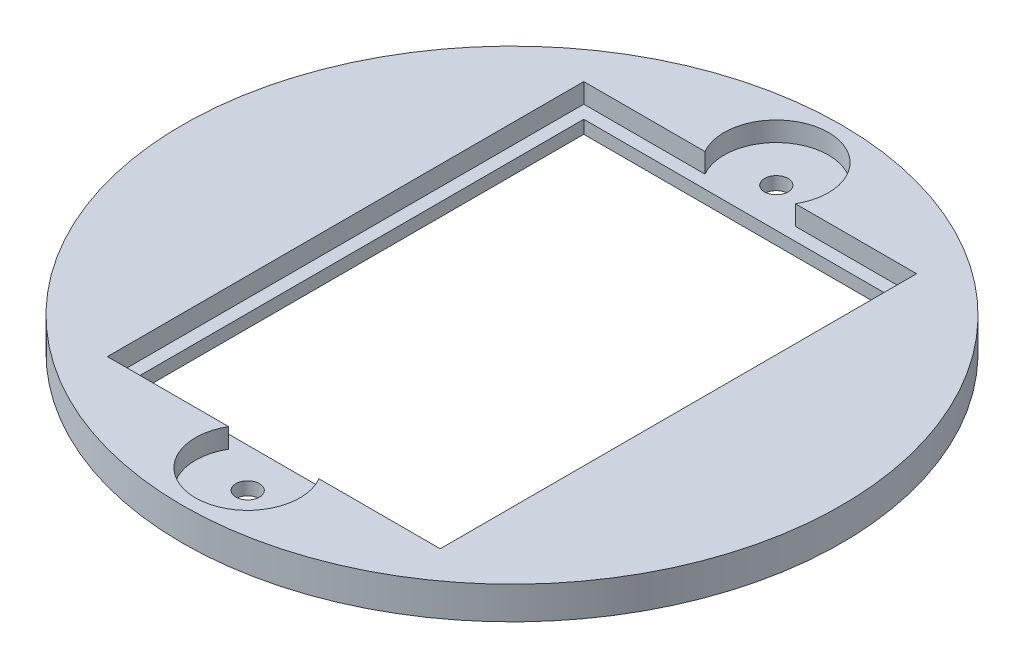
SolidWorks part; units mm, degrees
ref_plane "Front Plane" through (0, 0, 0) normal (0, 0, 1) x (1, 0, 0)
ref_plane "Top Plane" through (0, 0, 0) normal (0, 1, 0) x (1, 0, 0)
ref_plane "Right Plane" through (0, 0, 0) normal (1, 0, 0) x (0, 0, -1)
sketch "Sketch1" plane through (0, 0, 0) normal (0, 1, 0) x (1, 0, 0)
  circle A0 centre (0, 0) radius 25.25
extrude "Boss-Extrude1" add sketch "Sketch1" along normal blind 2.5
sketch "Sketch2" plane through (0, 2.5, 0) normal (0, 1, 0) x (1, 0, 0)
  line L1 (-12.75, 18.25) -> (12.75, 18.25)
  line L2 (-12.75, 18.25) -> (-12.75, -18.25)
  line L3 (-12.75, -18.25) -> (12.75, -18.25)
  line L4 (12.75, 18.25) -> (12.75, -18.25)
  line L5 (-12.75, 18.25) -> (12.75, -18.25) construction
  line L6 (-12.75, -18.25) -> (12.75, 18.25) construction
  point P0 (0, 0)
  dimension "D1" = 25.5
  dimension "D2" = 36.5
extrude "Cut-Extrude1" cut sketch "Sketch2" against normal blind 1.5
sketch "Sketch3" plane through (0, 1, 0) normal (0, 1, 0) x (1, 0, 0)
  line L1 (-11.75, 17.25) -> (11.75, 17.25)
  line L2 (-11.75, 17.25) -> (-11.75, -17.25)
  line L3 (-11.75, -17.25) -> (11.75, -17.25)
  line L4 (11.75, 17.25) -> (11.75, -17.25)
  line L5 (-11.75, 17.25) -> (11.75, -17.25) construction
  line L6 (-11.75, -17.25) -> (11.75, 17.25) construction
  point P0 (0, 0)
  dimension "D1" = 23.5
  dimension "D2" = 34.5
extrude "Cut-Extrude2" cut sketch "Sketch3" against normal blind 1.2
sketch "Sketch4" plane through (0, 2.5, 0) normal (0, 1, 0) x (1, 0, 0)
  line L0 (11.75, 17.25) -> (-11.75, 17.25) construction
  line L1 (-11.75, -17.25) -> (11.75, -17.25) construction
  circle A0 centre (0, 20.25) radius 4
  circle A1 centre (0, -20.25) radius 4
  point P4 (0, 17.25)
  point P8 (0, -17.25)
  dimension "D1" = 3
  dimension "D2" = 8
  dimension "D3" = 8
  dimension "D4" = 3
extrude "Cut-Extrude3" cut sketch "Sketch4" against normal blind 1.5
sketch "Sketch5" plane through (0, 1, 0) normal (0, 1, 0) x (1, 0, 0)
  circle A0 centre (0, 20.25) radius 0.9
  circle A1 centre (0, -20.25) radius 0.9
extrude "Cut-Extrude4" cut sketch "Sketch5" against normal through all
